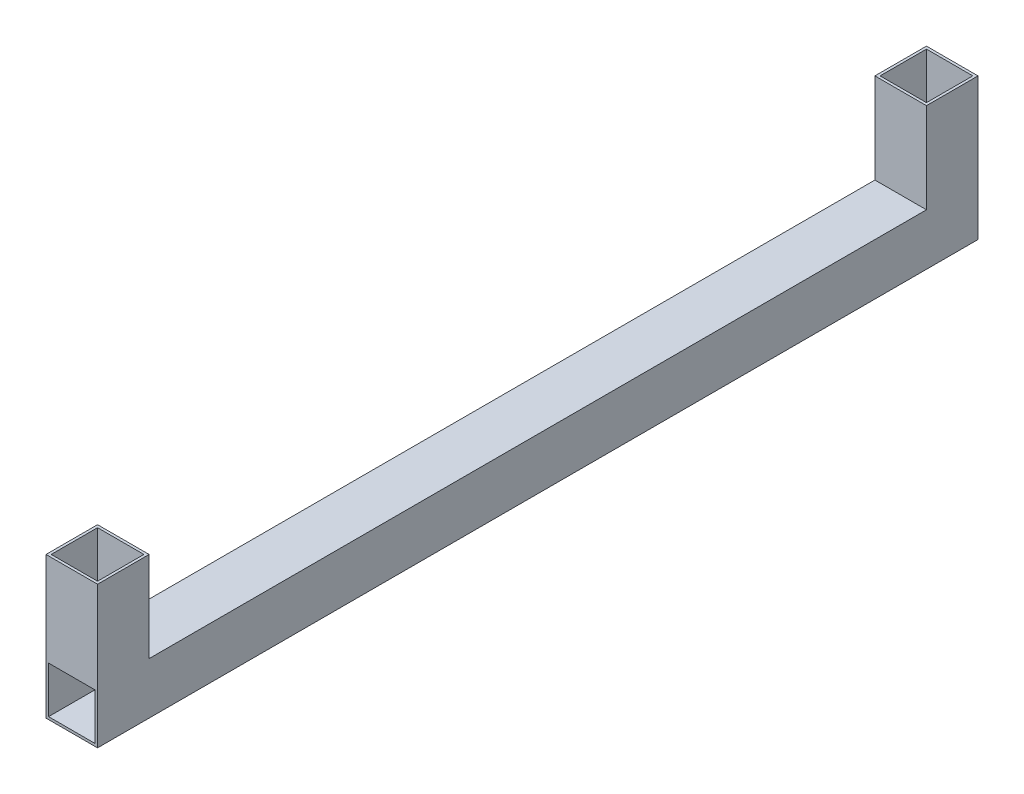
SolidWorks part; units mm, degrees
material "6061 Alloy"
ref_plane "Front Plane" through (0, 0, 0) normal (0, 0, 1) x (1, 0, 0)
ref_plane "Top Plane" through (0, 0, 0) normal (0, 1, 0) x (1, 0, 0)
ref_plane "Right Plane" through (0, 0, 0) normal (1, 0, 0) x (0, 0, -1)
sketch "Sketch2" plane through (0, 0, 0) normal (0, 0, 1) x (1, 0, 0)
  line L0 (-9, 9) -> (9, 9)
  line L1 (-10, -10) -> (10, -10)
  line L2 (-10, -10) -> (-10, 10)
  line L3 (-10, 10) -> (10, 10)
  line L4 (10, -10) -> (10, 10)
  line L5 (-10, -10) -> (10, 10) construction
  line L6 (-10, 10) -> (10, -10) construction
  line L7 (9, -9) -> (9, 9)
  line L8 (-9, -9) -> (9, -9)
  line L9 (-9, -9) -> (-9, 9)
  point P0 (0, 0)
  dimension "D1" = 20
  dimension "D2" = 20
  dimension "D3" = 1
extrude "Boss-Extrude1" add sketch "Sketch2" along normal blind 341.6
sketch "Sketch3" plane through (0, 10, 0) normal (0, 1, 0) x (1, 0, 0)
  line L0 (-10, 0) -> (10, 0)
  line L1 (-10, 0) -> (-10, -20)
  line L2 (10, 0) -> (10, -20)
  line L3 (-10, -20) -> (10, -20)
  line L4 (-10, -341.6) -> (10, -341.6)
  line L5 (-10, -341.6) -> (-10, -321.6)
  line L6 (10, -341.6) -> (10, -321.6)
  line L7 (-10, -321.6) -> (10, -321.6)
  line L8 (-9, -1) -> (9, -1)
  line L9 (9, -1) -> (9, -19)
  line L10 (-9, -19) -> (9, -19)
  line L11 (-9, -1) -> (-9, -19)
  line L12 (-9, -322.6) -> (9, -322.6)
  line L13 (9, -340.6) -> (9, -322.6)
  line L14 (-9, -340.6) -> (9, -340.6)
  line L15 (-9, -340.6) -> (-9, -322.6)
  dimension "D1" = 20
  dimension "D2" = 20
  dimension "D3" = 1
  dimension "D4" = 1
extrude "Boss-Extrude2" add sketch "Sketch3" along normal blind 35
